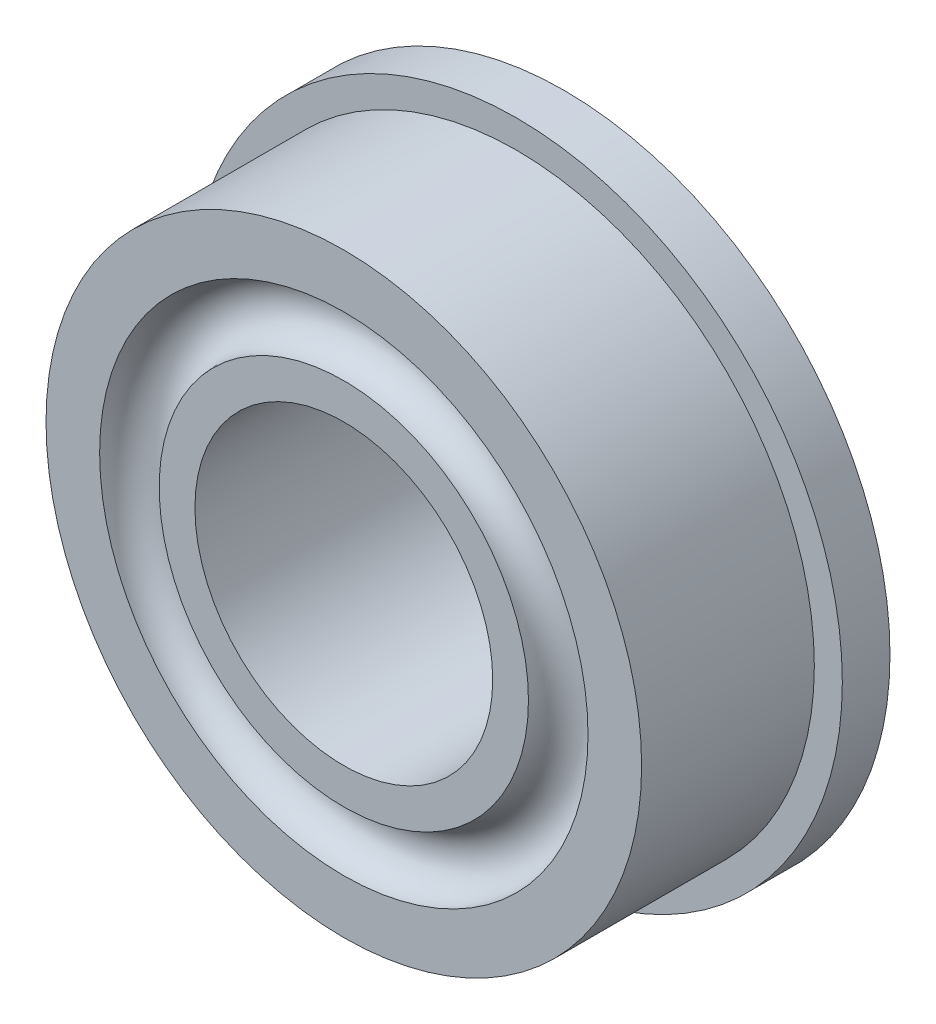
SolidWorks part; units mm, degrees
material "Plain Carbon Steel"
ref_plane "Front Plane" through (0, 0, 0) normal (0, 0, 1) x (1, 0, 0)
ref_plane "Top Plane" through (0, 0, 0) normal (0, 1, 0) x (1, 0, 0)
ref_plane "Right Plane" through (0, 0, 0) normal (1, 0, 0) x (0, 0, -1)
sketch "Sketch1" plane through (0, 0, 0) normal (0, 0, 1) x (1, 0, 0)
  circle A0 centre (0, 0) radius 6.9469
  circle A1 centre (0, 0) radius 3.175
  dimension "D1" = 13.8938
  dimension "D2" = 6.35
extrude "Boss-Extrude1" add sketch "Sketch1" along normal blind 1.016
sketch "Sketch2" plane through (0, 0, 1.016) normal (0, 0, 1) x (1, 0, 0)
  circle A0 centre (0, 0) radius 3.175
  circle A1 centre (0, 0) radius 6.35
  dimension "D1" = 6.35
  dimension "D2" = 12.7
extrude "Boss-Extrude2" add sketch "Sketch2" along normal blind 3.683
ref_axis "Axis1" through (0, 0, 4.699) along (0, 0, -1)
sketch "Sketch7" plane through (0, 0, 0) normal (1, 0, 0) x (0, 0, -1)
  line L0 (-4.699, 6.35) -> (-4.699, -6.35) construction
  line L1 (-4.699, 0) -> (0, 0) construction
  line L2 (-4.699, 5.207) -> (-4.699, 3.937)
  line L3 (0, -6.9469) -> (0, 6.9469) construction
  line L4 (0, 5.207) -> (0, 3.937)
  arc A0 (-4.699, 5.207) -> (-4.699, 3.937) centre (-4.699, 4.572) cw
  arc A1 (0, 5.207) -> (0, 3.937) centre (0, 4.572) ccw
  dimension "D1" = 0.635
  dimension "D3" = 0.635
  dimension "D2" = 4.572
  dimension "D4" = 4.572
revolve "Cut-Revolve2" cut sketch "Sketch7" angle 360 about axis through (0, 0, 4.699) along (0, 0, -1)
ref_plane "BEARING_MID_PLANE" through (0, 0, 2.3495) normal (0, 0, 1) x (1, 0, 0)
